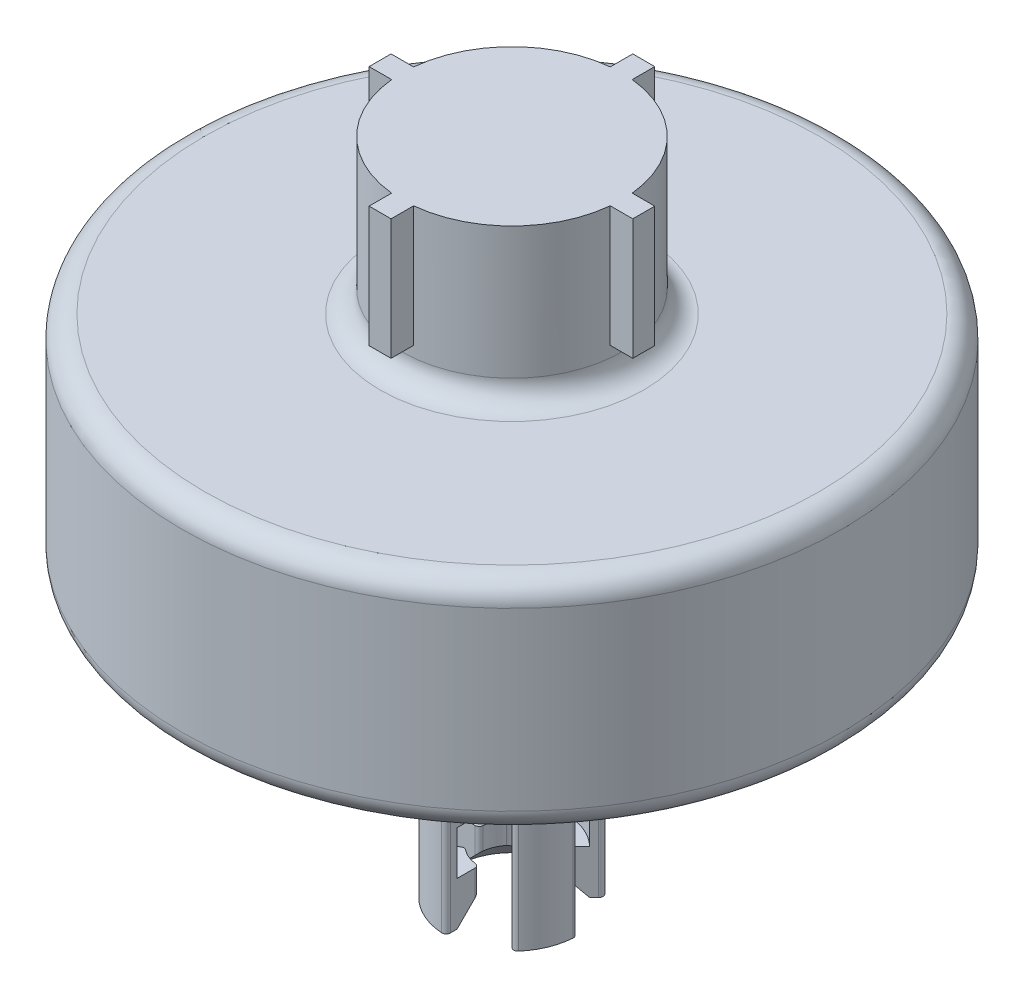
SolidWorks part; units mm, degrees
ref_plane "Front Plane" through (0, 0, 0) normal (0, 0, 1) x (1, 0, 0)
ref_plane "Top Plane" through (0, 0, 0) normal (0, 1, 0) x (1, 0, 0)
ref_plane "Right Plane" through (0, 0, 0) normal (1, 0, 0) x (0, 0, -1)
sketch "Sketch1" plane through (0, 0, 0) normal (0, 1, 0) x (1, 0, 0)
  circle A0 centre (0, 0) radius 150
extrude "Boss-Extrude2" add sketch "Sketch1" along normal blind 100
sketch "Sketch2" plane through (0, 100, 0) normal (0, 1, 0) x (1, 0, 0)
  circle A0 centre (0, 0) radius 50
  dimension "D1" = 100
extrude "Boss-Extrude3" add sketch "Sketch2" along normal blind 70
sketch "Sketch3" plane through (0, 0, 0) normal (0, 0, 1) x (1, 0, 0)
  line L0 (0, 170) -> (0, 100) construction
  line L1 (50, 170) -> (-50, 170) construction
  line L2 (150, 100) -> (-150, 100) construction
  line L3 (-5, 170) -> (-5, 115)
  line L4 (5, 170) -> (5, 115)
  line L5 (-5, 170) -> (5, 170)
  line L6 (-5, 115) -> (5, 115)
  line L8 (-5, 170) -> (-5, 100) construction
  line L9 (5, 170) -> (5, 100) construction
  dimension "D1" = 5
  dimension "D2" = 5
  dimension "D3" = 55
extrude "Boss-Extrude4" add sketch "Sketch3" along normal blind 60
pattern_circular "CirPattern1" count 4 over 360 about axis through (0, 0, 0) along (0, 1, 0) of "Boss-Extrude4"
sketch "Sketch4" plane through (0, 0, 0) normal (0, -1, 0) x (1, 0, 0)
  circle A0 centre (0, 0) radius 50
extrude "Boss-Extrude5" add sketch "Sketch4" along normal blind 50
sketch "Sketch5" plane through (0, -50, 0) normal (0, -1, 0) x (1, 0, 0)
  circle A0 centre (0, 0) radius 30
extrude "Boss-Extrude6" add sketch "Sketch5" along normal blind 80
sketch "Sketch6" plane through (0, -130, 0) normal (0, -1, 0) x (1, 0, 0)
  line L0 (0, 16.8819) -> (0, 27.9285)
  line L1 (11.9373, 11.9373) -> (19.7484, 19.7484)
  line L2 (16.8819, 0) -> (27.9285, 0)
  line L3 (11.9373, -11.9373) -> (19.7484, -19.7484)
  line L4 (0, -16.8819) -> (0, -27.9285)
  line L5 (-11.9373, -11.9373) -> (-19.7484, -19.7484)
  line L6 (-16.8819, 0) -> (-27.9285, 0)
  line L7 (-11.9373, 11.9373) -> (-19.7484, 19.7484)
  arc A0 (19.6438, -22.6742) -> (29.9234, 2.1429) centre (0, 0) ccw
  arc A2 (-1.7647, 14.8958) -> (-9.2851, 11.7808) centre (0, 0) ccw
  arc A3 (14.8958, 1.7647) -> (11.7808, 9.2851) centre (0, 0) ccw
  arc A5 (1.7647, -14.8958) -> (9.2851, -11.7808) centre (0, 0) ccw
  arc A8 (-14.8958, -1.7647) -> (-11.7808, -9.2851) centre (0, 0) ccw
  arc A9 (0, 16.8819) -> (-1.7647, 14.8958) centre (-2, 16.8819) cw
  arc A10 (-11.9373, 11.9373) -> (-9.2851, 11.7808) centre (-10.5231, 13.3515) ccw
  arc A11 (-16.8819, 0) -> (-14.8958, -1.7647) centre (-16.8819, -2) cw
  arc A12 (-11.9373, -11.9373) -> (-11.7808, -9.2851) centre (-13.3515, -10.5231) ccw
  arc A13 (0, -16.8819) -> (1.7647, -14.8958) centre (2, -16.8819) cw
  arc A14 (11.9373, -11.9373) -> (9.2851, -11.7808) centre (10.5231, -13.3515) ccw
  arc A15 (16.8819, 0) -> (14.8958, 1.7647) centre (16.8819, 2) cw
  arc A16 (11.9373, 11.9373) -> (11.7808, 9.2851) centre (13.3515, 10.5231) ccw
  arc A17 (19.7484, 19.7484) -> (22.6742, 19.6438) centre (21.1626, 18.3342) cw
  arc A18 (27.9285, 0) -> (29.9234, 2.1429) centre (27.9285, 2) ccw
  arc A19 (19.7484, -19.7484) -> (19.6438, -22.6742) centre (18.3342, -21.1626) cw
  arc A20 (0, -27.9285) -> (2.1429, -29.9234) centre (2, -27.9285) ccw
  arc A21 (-19.7484, -19.7484) -> (-22.6742, -19.6438) centre (-21.1626, -18.3342) cw
  arc A22 (-27.9285, 0) -> (-29.9234, -2.1429) centre (-27.9285, -2) ccw
  arc A23 (-19.7484, 19.7484) -> (-19.6438, 22.6742) centre (-18.3342, 21.1626) cw
  arc A24 (0, 27.9285) -> (-2.1429, 29.9234) centre (-2, 27.9285) ccw
  arc A25 (-19.6438, 22.6742) -> (-29.9234, -2.1429) centre (0, 0) ccw
  arc A26 (22.6742, 19.6438) -> (-2.1429, 29.9234) centre (0, 0) ccw
  arc A27 (-22.6742, -19.6438) -> (2.1429, -29.9234) centre (0, 0) ccw
  point P6 (0, 15)
  point P23 (0, 0)
  point P52 (0, 30)
  dimension "D1" = 8
  dimension "D2" = 2
extrude "Cut-Extrude2" cut sketch "Sketch6" against normal blind 80
ref_plane "Plane1" through (0, -130, 0) normal (0, -1, 0) x (-1, 0, 0)
ref_plane "Plane2" through (0, -110, 0) normal (0, -1, 0) x (-1, 0, 0)
sketch "Sketch7" plane through (0, -110, 0) normal (0, -1, 0) x (-1, 0, 0)
  circle A0 centre (0, 0) radius 25
  dimension "D1" = 50
extrude "Cut-Extrude3" cut sketch "Sketch7" against normal blind 20
sketch "Sketch8" plane through (0, -130, 0) normal (0, -1, 0) x (1, 0, 0)
  circle A0 centre (0, 0) radius 25
extrude "Cut-Extrude4" cut sketch "Sketch8" against normal blind 39 draft 45
fillet "Fillet1" radius 10 2 edges at (0, 0, 150) (0, 100, 150)
fillet "Fillet2" radius 10 1 edges at (0, -50, -50)
fillet "Fillet3" radius 10 1 edges at (0, 0, -50)
fillet "Fillet4" radius 10 1 edges at (0, 100, 50)
